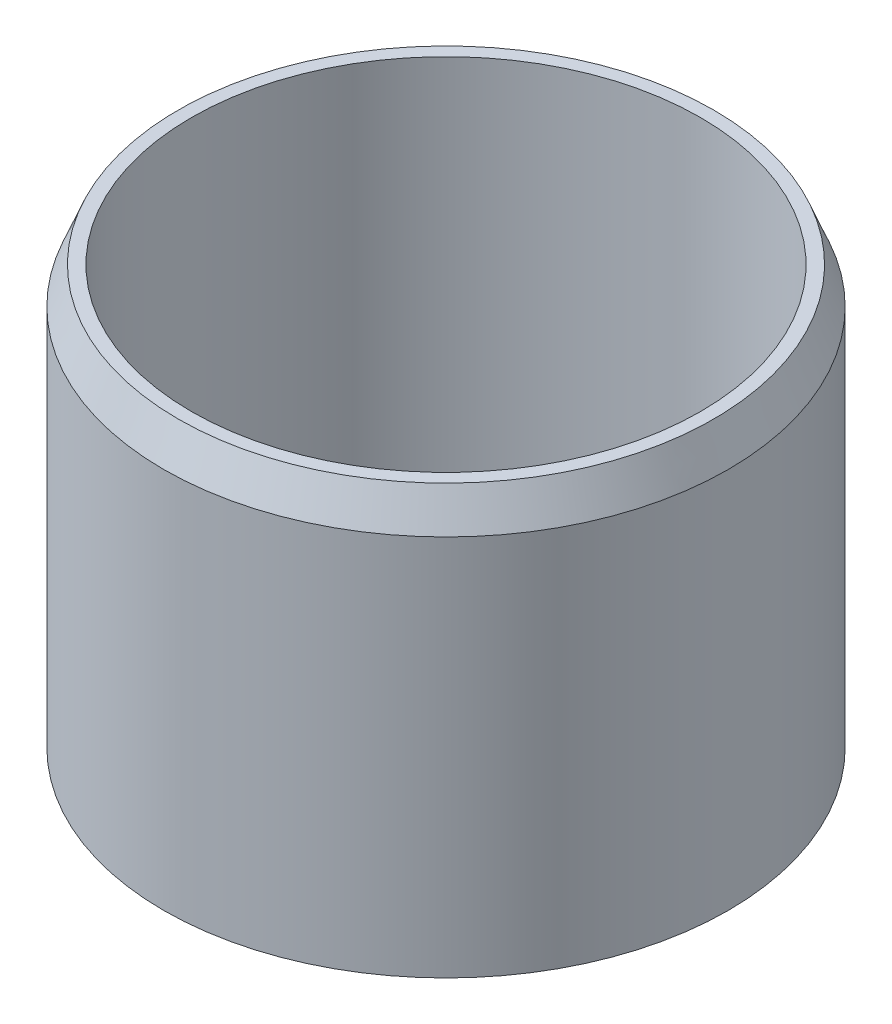
SolidWorks part; units mm, degrees
material "ABS"
ref_plane "Front Plane" through (0, 0, 0) normal (0, 0, 1) x (1, 0, 0)
ref_plane "Top Plane" through (0, 0, 0) normal (0, 1, 0) x (1, 0, 0)
ref_plane "Right Plane" through (0, 0, 0) normal (1, 0, 0) x (0, 0, -1)
sketch "Sketch1" plane through (0, 0, 0) normal (0, 1, 0) x (1, 0, 0)
  line L6 (0, 12.7) -> (0, 44.45)
  circle A0 centre (0, 0) radius 49.276
  circle A1 centre (0, 0) radius 6.5024
  circle A2 centre (0, 0) radius 12.7
  circle A3 centre (0, 0) radius 44.45
  circle A4 centre (0, 28.575) radius 12.7
  circle A5 centre (27.1764, 8.8302) radius 12.7
  circle A6 centre (16.796, -23.1177) radius 12.7
  circle A7 centre (-16.796, -23.1177) radius 12.7
  circle A8 centre (-27.1764, 8.8302) radius 12.7
  point P26 (0, 0)
  dimension "D1" = 98.552
  dimension "D2" = 13.0048
  dimension "D6" = 25.4
  dimension "D7" = 88.9
  dimension "D8" = 25.4
  dimension "D9" = 5
extrude "Boss-Extrude1" add sketch "Sketch1" along normal blind 9.525
sketch "Sketch2" plane through (0, 9.525, 0) normal (0, 1, 0) x (1, 0, 0)
  circle A0 centre (0, 0) radius 49.276
  circle A1 centre (0, 0) radius 44.45
  dimension "D1" = 98.552
  dimension "D2" = 88.9
extrude "Boss-Extrude2" add sketch "Sketch2" along normal blind 63.5
sketch "Sketch3" plane through (0, 9.525, 0) normal (0, 1, 0) x (1, 0, 0)
  circle A0 centre (0, 0) radius 12.7
  circle A2 centre (0, 0) radius 6.5024
  dimension "D1" = 25.4
  dimension "D2" = 13.0048
extrude "Boss-Extrude3" add sketch "Sketch3" along normal blind 15.875
chamfer "Chamfer1" distance 6.35 distance2 2.54 1 edges at (0, 73.025, 49.276)
sketch "Sketch4" plane through (0, 25.4, 0) normal (0, 1, 0) x (1, 0, 0)
  circle A0 centre (0, 0) radius 12.7
  dimension "D1" = 25.4
extrude "Boss-Extrude4" add sketch "Sketch4" along normal blind 6.35
fillet "Fillet1" radius 2.54 1 edges at (0, 31.75, 12.7)
